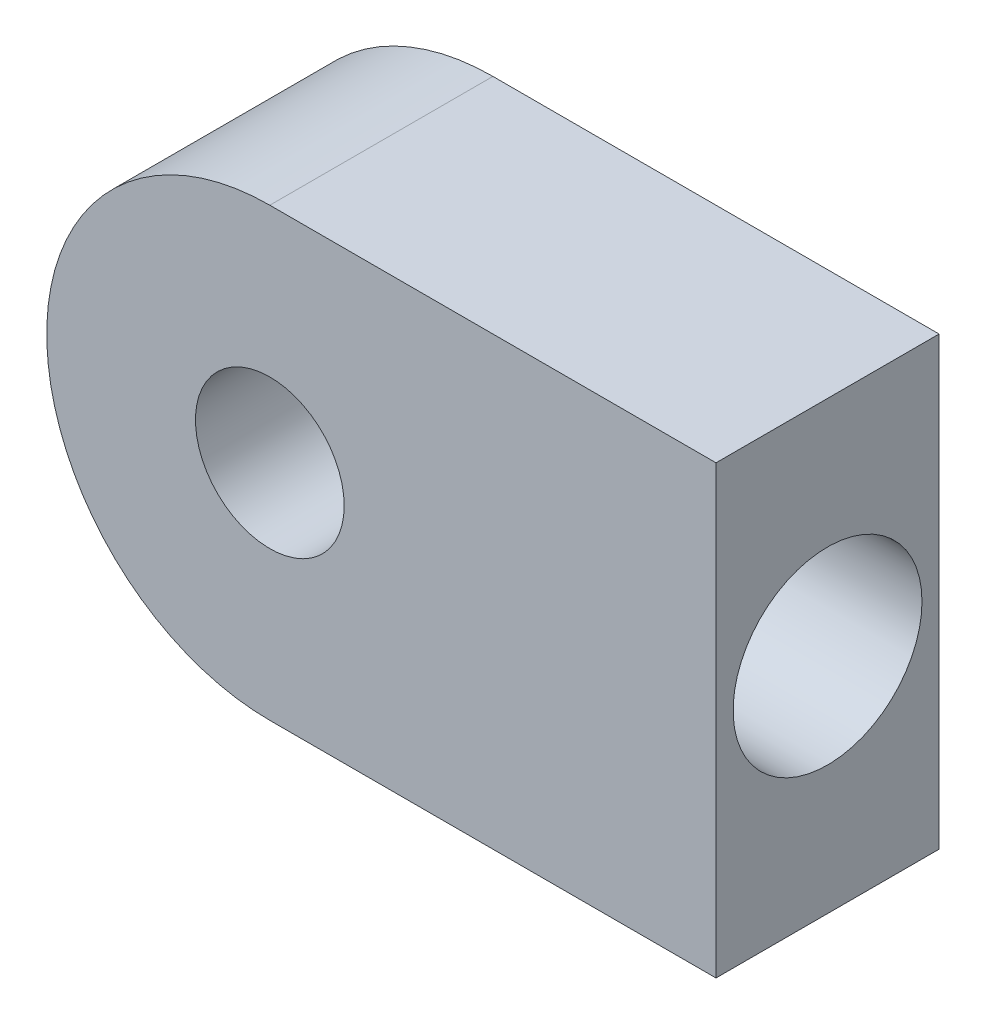
SolidWorks part; units mm, degrees
material "6063-T5"
ref_plane "Front Plane" through (0, 0, 0) normal (0, 0, 1) x (1, 0, 0)
ref_plane "Top Plane" through (0, 0, 0) normal (0, 1, 0) x (1, 0, 0)
ref_plane "Right Plane" through (0, 0, 0) normal (1, 0, 0) x (0, 0, -1)
sketch "Sketch1" plane through (0, 0, 0) normal (0, 0, 1) x (1, 0, 0)
  line L0 (0, 15) -> (30, 15)
  line L1 (30, 15) -> (30, -15)
  line L2 (30, -15) -> (0, -15)
  arc A0 (0, 15) -> (0, -15) centre (0, 0) ccw
  circle A1 centre (0, 0) radius 5
  dimension "D1" = 30
  dimension "D2" = 10
  dimension "D3" = 30
extrude "Boss-Extrude1" add sketch "Sketch1" along normal mid plane 15
sketch "Sketch2" plane through (30, 0, 0) normal (1, 0, 0) x (0, 0, -1)
  circle A0 centre (0, 0) radius 6.35
  dimension "D1" = 12.7
extrude "Cut-Extrude1" cut sketch "Sketch2" against normal blind 20
